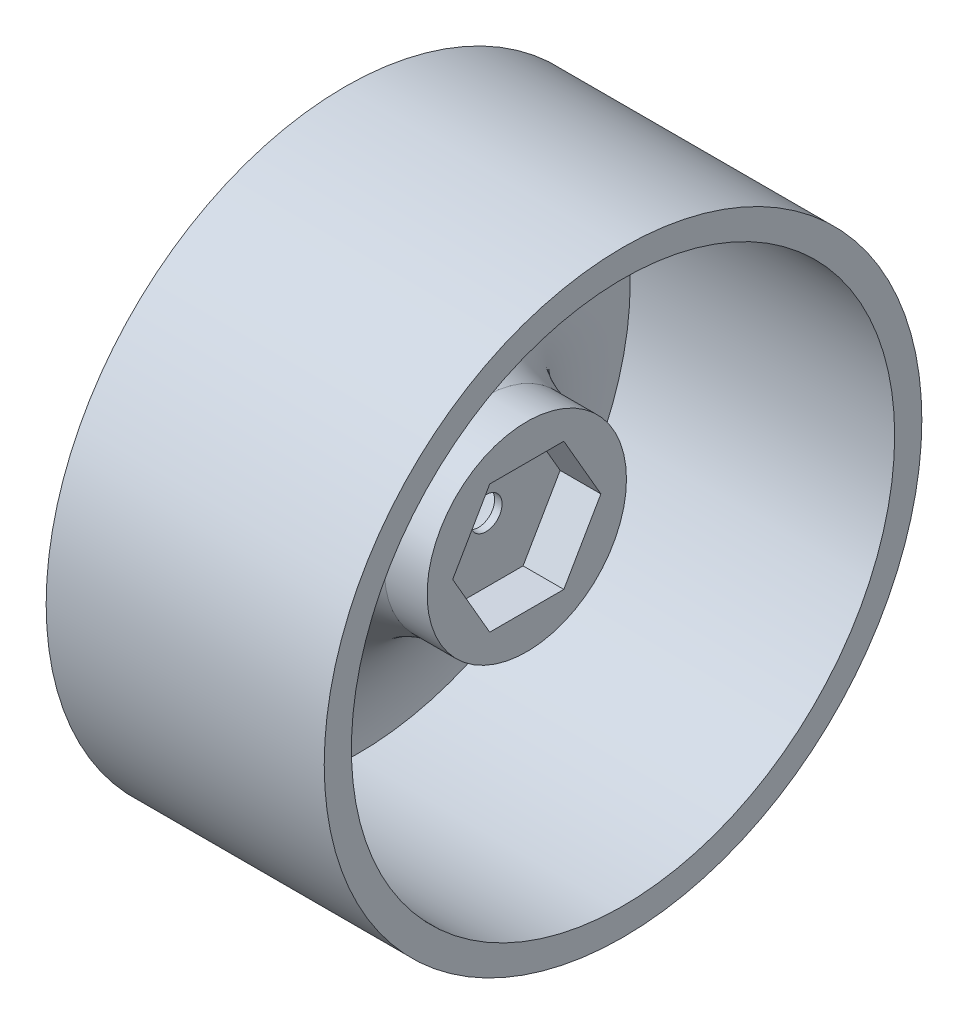
SolidWorks part; units mm, degrees
ref_plane "Front Plane" through (0, 0, 0) normal (0, 0, 1) x (1, 0, 0)
ref_plane "Top Plane" through (0, 0, 0) normal (0, 1, 0) x (1, 0, 0)
ref_plane "Right Plane" through (0, 0, 0) normal (1, 0, 0) x (0, 0, -1)
sketch "Reference" plane through (0, 0, 0) normal (0, 1, 0) x (1, 0, 0)
  line L0 (0, 25.4) -> (0, 0) construction
  line L5 (-13, -27.94) -> (13, -27.94) construction
  line L6 (-13, -27.94) -> (-13, 27.94) construction
  line L7 (-13, 27.94) -> (13, 27.94) construction
  line L8 (13, 25.4) -> (13, 27.94) construction
  line L9 (-13, -27.94) -> (13, 27.94) construction
  line L10 (-13, 27.94) -> (13, -27.94) construction
  line L11 (-13, 27.94) -> (13, 27.94) construction
  line L12 (-13, 25.4) -> (13, 25.4) construction
  line L13 (0, 8.0505) -> (0, 0) construction
  line L14 (0, 8.0505) -> (4, 8.0505) construction
  line L15 (-13, 25.4) -> (13, 25.4) construction
  line L16 (0, 9.3205) -> (4, 9.3205) construction
  line L17 (-0.508, 8.128) -> (-0.508, 0) construction
  spline S0 degree 2 poles (-13, 25.4) (-9.6405, 6.45) (4, 8.0505) knots 0 0 0 1 1 1 construction
  spline S1 degree 2 poles (0, 9.3205) (-9.3141, 10.672) (-11.73, 25.4) knots 0 0 0 1 1 1 construction
  point P0 (0, 0)
  dimension "D8" = 0.508
  dimension "D1" = 26
  dimension "D2" = 55.88
  dimension "D3" = 2.54
  dimension "D4" = 8.128
  dimension "D5" = 4
  dimension "D6" = 1.27
  dimension "D7" = 1.27
sketch "Sketch2" plane through (0, 0, 0) normal (0, 1, 0) x (1, 0, 0)
  line L3 (4, 8.0505) -> (4, 9.3205)
  line L4 (4, 9.3205) -> (0, 9.3205)
  line L5 (-0.508, 8.128) -> (-0.508, 0)
  line L7 (-13, 25.4) -> (-13, 27.94)
  line L8 (-13, 27.94) -> (13, 27.94)
  line L9 (13, 27.94) -> (13, 25.4)
  line L11 (-11.73, 25.4) -> (13, 25.4)
  line L12 (4, 8.0505) -> (4, 0)
  line L13 (4, 0) -> (-0.508, 0)
  spline S0 degree 2 poles (-0.508, 8.128) (-13.1591, 7.3367) (-13, 25.4) knots 0 0 0 1 1 1
  spline S1 degree 3 poles (-11.73, 25.4) (-11.9399, 16.186) (-5.7676, 10.5735) (0, 9.3205) knots 0 0 0 0 1 1 1 1
revolve "Main Revolve" add sketch "Sketch2" angle 360 about L13
sketch "Sketch5" plane through (4, 0, 0) normal (1, 0, 0) x (0, 0, -1)
  line L1 (6.9282, 0) -> (3.4641, 6)
  line L2 (3.4641, 6) -> (-3.4641, 6)
  line L3 (-3.4641, 6) -> (-6.9282, 0)
  line L4 (-6.9282, 0) -> (-3.4641, -6)
  line L5 (-3.4641, -6) -> (3.4641, -6)
  line L6 (3.4641, -6) -> (6.9282, 0)
  circle A0 centre (0, 0) radius 6 construction
  dimension "D1" = 12
extrude "Cut-Extrude1" cut sketch "Sketch5" against normal blind 3.81
sketch "Sketch6" plane through (-0.508, 0, 0) normal (-1, 0, 0) x (0, 0, 1)
  circle A0 centre (0, 0) radius 1.5
  dimension "D1" = 3
extrude "Cut-Extrude2" cut sketch "Sketch6" against normal through all
